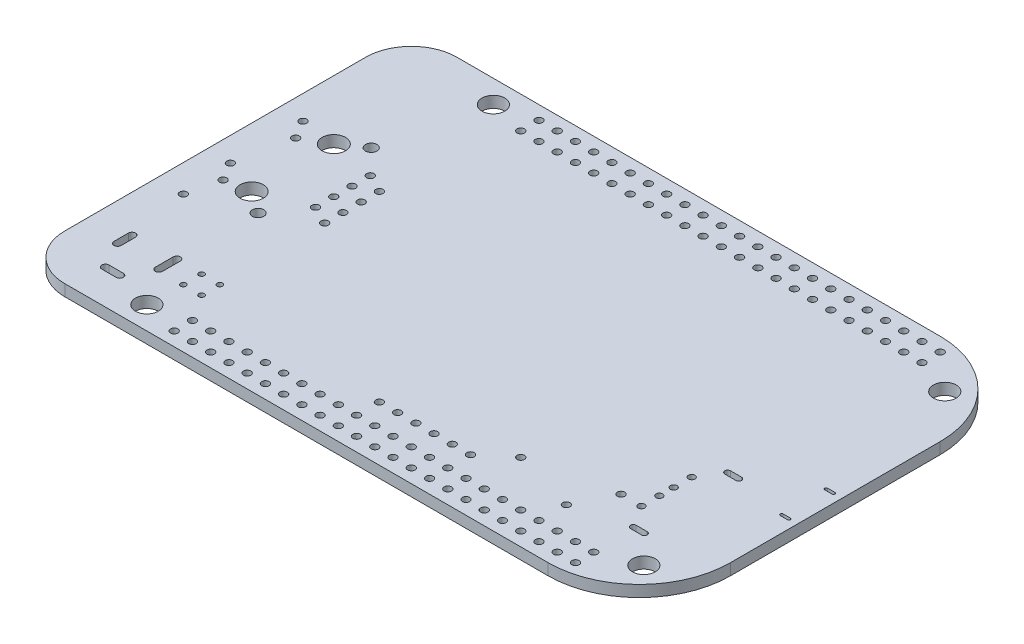
SolidWorks part; units mm, degrees
ref_plane "Front" through (0, 0, 0) normal (0, 0, 1) x (1, 0, 0)
ref_plane "Top" through (0, 0, 0) normal (0, 1, 0) x (1, 0, 0)
ref_plane "Right" through (0, 0, 0) normal (1, 0, 0) x (0, 0, -1)
sketch "Sketch2" plane through (0, 0, 0) normal (0, 1, 0) x (1, 0, 0)
  line L1 (-43.18, 27.305) -> (43.18, 27.305)
  line L2 (-43.18, 27.305) -> (-43.18, -27.305)
  line L3 (-43.18, -27.305) -> (43.18, -27.305)
  line L4 (43.18, 27.305) -> (43.18, -27.305)
  line L5 (-43.18, 27.305) -> (43.18, -27.305) construction
  line L6 (-43.18, -27.305) -> (43.18, 27.305) construction
  point P0 (0, 0)
  dimension "D1" = 86.36
  dimension "D2" = 54.61
extrude "Main Board" add sketch "Sketch2" along normal mid plane 1.5875 separate body
sketch "Sketch3" plane through (0, -0.7937, 0) normal (0, -1, 0) x (1, 0, 0)
  line L2 (43.18, -27.305) -> (-43.18, -27.305) construction
  line L3 (-43.18, -27.305) -> (-43.18, 27.305) construction
  circle A0 centre (37.465, 20.955) radius 1.5875
  circle A1 centre (37.465, -20.955) radius 1.5875
  circle A2 centre (-28.575, -24.13) radius 1.5875
  circle A3 centre (-28.575, 24.13) radius 1.5875
  dimension "D1" = 3.175
  dimension "D2" = 14.605
  dimension "D3" = 66.04
  dimension "D4" = 48.26
  dimension "D5" = 51.435
  dimension "D6" = 6.35
  dimension "D7" = 3.175
extrude "Board Mounting Holes" cut sketch "Sketch3" against normal through all contours A3 | A2 | A1 | A0
sketch "Sketch4" plane through (0, -0.7937, 0) normal (0, -1, 0) x (1, 0, 0)
  line L0 (-39.8272, -8.8646) -> (-39.8272, 1.2446) construction
  line L1 (-38.3032, -6.3246) -> (-38.3032, 3.7846) construction
  line L2 (-34.925, 3.175) -> (-34.925, -8.255) construction
  line L3 (-31.877, 5.334) -> (-31.877, -10.414) construction
  line L4 (-28.575, -6.985) -> (-28.575, 0.635) construction
  line L5 (-26.035, -5.715) -> (-26.035, 1.905) construction
  line L6 (43.18, -27.305) -> (-43.18, -27.305) construction
  line L7 (-43.18, -27.305) -> (-43.18, 27.305) construction
  circle A1 centre (-38.3032, 3.7846) radius 0.508
  circle A2 centre (-39.8272, 1.2446) radius 0.508
  circle A3 centre (-38.3032, -6.3246) radius 0.508
  circle A4 centre (-39.8272, -8.8646) radius 0.508
  circle A5 centre (-28.575, -6.985) radius 0.508
  circle A6 centre (-28.575, -4.445) radius 0.508
  circle A7 centre (-28.575, -1.905) radius 0.508
  circle A8 centre (-28.575, 0.635) radius 0.508
  circle A9 centre (-26.035, 1.905) radius 0.508
  circle A10 centre (-26.035, -0.635) radius 0.508
  circle A11 centre (-26.035, -3.175) radius 0.508
  circle A12 centre (-26.035, -5.715) radius 0.508
  circle A13 centre (-31.877, 5.334) radius 0.8001
  circle A14 centre (-34.925, 3.175) radius 1.6256
  circle A15 centre (-34.925, -8.255) radius 1.6256
  circle A16 centre (-31.877, -10.414) radius 0.8001
  dimension "D1" = 1.016
  dimension "D2" = 3.2512
  dimension "D3" = 1.6002
  dimension "D4" = 18.4404
  dimension "D5" = 10.1092
  dimension "D6" = 3.3528
  dimension "D7" = 4.8768
  dimension "D8" = 8.255
  dimension "D9" = 11.303
  dimension "D10" = 14.605
  dimension "D11" = 17.145
  dimension "D12" = 11.43
  dimension "D13" = 15.748
  dimension "D14" = 10.1092
  dimension "D15" = 20.9804
  dimension "D16" = 19.05
  dimension "D17" = 16.891
  dimension "D18" = 20.32
  dimension "D19" = 7.62
  dimension "D20" = 21.59
  dimension "D21" = 7.62
  dimension "D22" = 2.54
  dimension "D23" = 2.54
  dimension "D24" = 5.08
  dimension "D25" = 5.08
extrude "P5 - Ethernet Connector Holes" cut sketch "Sketch4" against normal through all
sketch "Sketch5" plane through (0, -0.7937, 0) normal (0, -1, 0) x (1, 0, 0)
  line L0 (30.1602, 13.9878) -> (30.1602, 6.9875) construction
  line L1 (43.18, -27.305) -> (-43.18, -27.305) construction
  line L2 (-43.18, -27.305) -> (-43.18, 27.305) construction
  line L3 (32.1004, 17.0577) -> (33.6404, 17.0577) construction
  line L4 (32.1004, 17.4545) -> (33.6404, 17.4545)
  line L5 (32.1004, 16.6608) -> (33.6404, 16.6608)
  line L6 (32.1004, 3.9177) -> (33.6404, 3.9177) construction
  line L7 (32.1004, 4.3145) -> (33.6404, 4.3145)
  line L8 (32.1004, 3.5208) -> (33.6404, 3.5208)
  circle A0 centre (30.1602, 13.9878) radius 0.46
  circle A1 centre (30.1602, 11.4884) radius 0.46
  circle A2 centre (30.1602, 9.4869) radius 0.46
  circle A3 centre (30.1602, 6.9875) radius 0.46
  arc A4 (32.1004, 17.4545) -> (32.1004, 16.6608) centre (32.1004, 17.0577) ccw
  arc A5 (33.6404, 16.6608) -> (33.6404, 17.4545) centre (33.6404, 17.0577) ccw
  arc A7 (32.1004, 4.3145) -> (32.1004, 3.5208) centre (32.1004, 3.9177) ccw
  arc A8 (33.6404, 3.5208) -> (33.6404, 4.3145) centre (33.6404, 3.9177) ccw
  point P16 (32.8704, 17.0577)
  point P23 (32.8704, 3.9177)
  dimension "D6" = 0.92
  dimension "D7" = 0.3969
  dimension "D1" = 2.4994
  dimension "D2" = 2.0015
  dimension "D3" = 2.4994
  dimension "D4" = 34.2925
  dimension "D5" = 73.3402
  dimension "D8" = 13.14
  dimension "D9" = 1.54
  dimension "D10" = 75.2804
  dimension "D11" = 31.2227
extrude "P3 - USB Host" cut sketch "Sketch5" against normal through all
sketch "Sketch6" plane through (0, -0.7937, 0) normal (0, -1, 0) x (1, 0, 0)
  line L0 (40.9621, 5.2591) -> (41.9781, 5.2591) construction
  line L1 (40.9621, 5.4575) -> (41.9781, 5.4575)
  line L2 (40.9621, 5.0606) -> (41.9781, 5.0606)
  line L3 (40.9621, -0.9411) -> (41.9781, -0.9411) construction
  line L4 (40.9621, -0.7426) -> (41.9781, -0.7426)
  line L5 (40.9621, -1.1395) -> (41.9781, -1.1395)
  line L6 (43.18, -27.305) -> (-43.18, -27.305) construction
  line L7 (-43.18, -27.305) -> (-43.18, 27.305) construction
  line L8 (41.4701, 5.2591) -> (41.4701, -0.9411) construction
  arc A0 (40.9621, 5.4575) -> (40.9621, 5.0606) centre (40.9621, 5.2591) ccw
  arc A1 (41.9781, 5.0606) -> (41.9781, 5.4575) centre (41.9781, 5.2591) ccw
  arc A2 (40.9621, -0.7426) -> (40.9621, -1.1395) centre (40.9621, -0.9411) ccw
  arc A3 (41.9781, -1.1395) -> (41.9781, -0.7426) centre (41.9781, -0.9411) ccw
  point P4 (41.4701, 5.2591)
  point P13 (41.4701, -0.9411)
  dimension "D1" = 0.1984
  dimension "D2" = 26.3639
  dimension "D3" = 6.2001
  dimension "D4" = 1.016
  dimension "D5" = 84.1421
extrude "P6 - HDMI" cut sketch "Sketch6" against normal through all
sketch "Sketch7" plane through (0, -0.7937, 0) normal (0, -1, 0) x (1, 0, 0)
  line L0 (-43.18, -27.305) -> (-43.18, 27.305) construction
  line L1 (43.18, -27.305) -> (-43.18, -27.305) construction
  circle A0 centre (32.385, 25.4) radius 0.51
  circle A2 centre (29.845, 25.4) radius 0.51
  circle A3 centre (27.305, 25.4) radius 0.51
  circle A4 centre (24.765, 25.4) radius 0.51
  circle A5 centre (22.225, 25.4) radius 0.51
  circle A6 centre (19.685, 25.4) radius 0.51
  circle A7 centre (17.145, 25.4) radius 0.51
  circle A8 centre (14.605, 25.4) radius 0.51
  circle A9 centre (12.065, 25.4) radius 0.51
  circle A10 centre (9.525, 25.4) radius 0.51
  circle A11 centre (6.985, 25.4) radius 0.51
  circle A12 centre (4.445, 25.4) radius 0.51
  circle A13 centre (1.905, 25.4) radius 0.51
  circle A14 centre (-0.635, 25.4) radius 0.51
  circle A15 centre (-3.175, 25.4) radius 0.51
  circle A16 centre (-5.715, 25.4) radius 0.51
  circle A17 centre (-8.255, 25.4) radius 0.51
  circle A18 centre (-10.795, 25.4) radius 0.51
  circle A19 centre (-13.335, 25.4) radius 0.51
  circle A20 centre (-15.875, 25.4) radius 0.51
  circle A21 centre (-18.415, 25.4) radius 0.51
  circle A22 centre (-20.955, 25.4) radius 0.51
  circle A23 centre (-23.495, 25.4) radius 0.51
  circle A24 centre (29.845, 22.86) radius 0.51
  circle A25 centre (27.305, 22.86) radius 0.51
  circle A26 centre (24.765, 22.86) radius 0.51
  circle A27 centre (22.225, 22.86) radius 0.51
  circle A28 centre (19.685, 22.86) radius 0.51
  circle A29 centre (17.145, 22.86) radius 0.51
  circle A30 centre (14.605, 22.86) radius 0.51
  circle A31 centre (12.065, 22.86) radius 0.51
  circle A32 centre (9.525, 22.86) radius 0.51
  circle A33 centre (6.985, 22.86) radius 0.51
  circle A34 centre (4.445, 22.86) radius 0.51
  circle A35 centre (1.905, 22.86) radius 0.51
  circle A36 centre (-0.635, 22.86) radius 0.51
  circle A37 centre (-3.175, 22.86) radius 0.51
  circle A38 centre (-5.715, 22.86) radius 0.51
  circle A39 centre (-8.255, 22.86) radius 0.51
  circle A40 centre (-10.795, 22.86) radius 0.51
  circle A41 centre (-13.335, 22.86) radius 0.51
  circle A42 centre (-15.875, 22.86) radius 0.51
  circle A43 centre (-18.415, 22.86) radius 0.51
  circle A44 centre (-20.955, 22.86) radius 0.51
  circle A45 centre (-23.495, 22.86) radius 0.51
  circle A46 centre (32.385, 22.86) radius 0.51
  dimension "D1" = 1.02
  dimension "D2" = 75.565
  dimension "D3" = 52.705
  dimension "D4" = 23
  dimension "D5" = 2
extrude "P9 - IDC Expansion Port" cut sketch "Sketch7" against normal through all contours A21
sketch "Sketch8" plane through (0, -0.7937, 0) normal (0, -1, 0) x (1, 0, 0)
  line L0 (43.18, -27.305) -> (-43.18, -27.305) construction
  line L1 (-43.18, -27.305) -> (-43.18, 27.305) construction
  circle A0 centre (32.385, -22.86) radius 0.51
  circle A1 centre (29.845, -22.86) radius 0.51
  circle A2 centre (27.305, -22.86) radius 0.51
  circle A3 centre (24.765, -22.86) radius 0.51
  circle A4 centre (22.225, -22.86) radius 0.51
  circle A5 centre (19.685, -22.86) radius 0.51
  circle A6 centre (17.145, -22.86) radius 0.51
  circle A7 centre (14.605, -22.86) radius 0.51
  circle A8 centre (12.065, -22.86) radius 0.51
  circle A9 centre (9.525, -22.86) radius 0.51
  circle A10 centre (6.985, -22.86) radius 0.51
  circle A11 centre (4.445, -22.86) radius 0.51
  circle A12 centre (1.905, -22.86) radius 0.51
  circle A13 centre (-0.635, -22.86) radius 0.51
  circle A14 centre (-3.175, -22.86) radius 0.51
  circle A15 centre (-5.715, -22.86) radius 0.51
  circle A16 centre (-8.255, -22.86) radius 0.51
  circle A17 centre (-10.795, -22.86) radius 0.51
  circle A18 centre (-13.335, -22.86) radius 0.51
  circle A19 centre (-15.875, -22.86) radius 0.51
  circle A20 centre (-18.415, -22.86) radius 0.51
  circle A21 centre (-20.955, -22.86) radius 0.51
  circle A22 centre (-23.495, -22.86) radius 0.51
  circle A23 centre (29.845, -25.4) radius 0.51
  circle A24 centre (27.305, -25.4) radius 0.51
  circle A25 centre (24.765, -25.4) radius 0.51
  circle A26 centre (22.225, -25.4) radius 0.51
  circle A27 centre (19.685, -25.4) radius 0.51
  circle A28 centre (17.145, -25.4) radius 0.51
  circle A29 centre (14.605, -25.4) radius 0.51
  circle A30 centre (12.065, -25.4) radius 0.51
  circle A31 centre (9.525, -25.4) radius 0.51
  circle A32 centre (6.985, -25.4) radius 0.51
  circle A33 centre (4.445, -25.4) radius 0.51
  circle A34 centre (1.905, -25.4) radius 0.51
  circle A35 centre (-0.635, -25.4) radius 0.51
  circle A36 centre (-3.175, -25.4) radius 0.51
  circle A37 centre (-5.715, -25.4) radius 0.51
  circle A38 centre (-8.255, -25.4) radius 0.51
  circle A39 centre (-10.795, -25.4) radius 0.51
  circle A40 centre (-13.335, -25.4) radius 0.51
  circle A41 centre (-15.875, -25.4) radius 0.51
  circle A42 centre (-18.415, -25.4) radius 0.51
  circle A43 centre (-20.955, -25.4) radius 0.51
  circle A44 centre (-23.495, -25.4) radius 0.51
  circle A45 centre (32.385, -25.4) radius 0.51
  dimension "D1" = 1.02
  dimension "D2" = 4.445
  dimension "D3" = 75.565
  dimension "D4" = 23
  dimension "D5" = 2
extrude "P8 - IDC Expansion Port" cut sketch "Sketch8" against normal through all
sketch "Sketch9" plane through (0, -0.7937, 0) normal (0, -1, 0) x (1, 0, 0)
  line L0 (43.18, -27.305) -> (-43.18, -27.305) construction
  line L1 (-43.18, -27.305) -> (-43.18, 27.305) construction
  circle A0 centre (15.875, 16.51) radius 0.508
  dimension "D1" = 1.016
  dimension "D2" = 43.815
  dimension "D3" = 59.055
extrude "TP1 - Test Point 1" cut sketch "Sketch9" against normal through all
sketch "Sketch10" plane through (0, -0.7937, 0) normal (0, -1, 0) x (1, 0, 0)
  line L0 (-43.18, -27.305) -> (-43.18, 27.305) construction
  line L2 (-43.18, 27.305) -> (43.18, 27.305) construction
  circle A0 centre (-39.37, 8.255) radius 0.508
  dimension "D3" = 1.016
  dimension "D1" = 3.81
  dimension "D2" = 19.05
extrude "TP4 - Test Point 4" cut sketch "Sketch10" against normal through all
sketch "Sketch11" plane through (0, -0.7937, 0) normal (0, -1, 0) x (1, 0, 0)
  line L0 (-43.18, 27.305) -> (43.18, 27.305) construction
  line L1 (-43.18, -27.305) -> (-43.18, 27.305) construction
  circle A0 centre (27.305, 13.97) radius 0.508
  circle A1 centre (24.765, 19.05) radius 0.508
  dimension "D1" = 1.016
  dimension "D2" = 5.08
  dimension "D3" = 2.54
  dimension "D4" = 8.255
  dimension "D5" = 67.945
extrude "RT1 - Capacitor" cut sketch "Sketch11" against normal through all
sketch "Sketch12" plane through (0, -0.7937, 0) normal (0, -1, 0) x (1, 0, 0)
  line L0 (-43.18, 27.305) -> (43.18, 27.305) construction
  line L1 (-43.18, -27.305) -> (-43.18, 27.305) construction
  circle A0 centre (12.065, 19.685) radius 0.508
  circle A1 centre (9.525, 19.685) radius 0.508
  circle A2 centre (6.985, 19.685) radius 0.508
  circle A3 centre (4.445, 19.685) radius 0.508
  circle A4 centre (1.905, 19.685) radius 0.508
  circle A5 centre (-0.635, 19.685) radius 0.508
  dimension "D1" = 1.016
  dimension "D2" = 7.62
  dimension "D3" = 55.245
  dimension "D4" = 6
extrude "J1 - Debug Port" cut sketch "Sketch12" against normal through all
sketch "Sketch13" plane through (0, -0.7937, 0) normal (0, -1, 0) x (1, 0, 0)
  line L0 (-32.004, 19.03) -> (-32.004, 16.53) construction
  line L1 (-31.5036, 19.03) -> (-31.5036, 16.53)
  line L2 (-32.5044, 19.03) -> (-32.5044, 16.53)
  line L3 (-37.9984, 16.78) -> (-37.9984, 18.78) construction
  line L4 (-38.4984, 16.78) -> (-38.4984, 18.78)
  line L5 (-37.4984, 16.78) -> (-37.4984, 18.78)
  line L6 (-36.0012, 22.479) -> (-34.0012, 22.479) construction
  line L7 (-36.0012, 22.9794) -> (-34.0012, 22.9794)
  line L8 (-36.0012, 21.9786) -> (-34.0012, 21.9786)
  line L9 (-43.18, 27.305) -> (43.18, 27.305) construction
  line L10 (-43.18, -27.305) -> (-43.18, 27.305) construction
  arc A0 (-31.5036, 19.03) -> (-32.5044, 19.03) centre (-32.004, 19.03) ccw
  arc A1 (-32.5044, 16.53) -> (-31.5036, 16.53) centre (-32.004, 16.53) ccw
  arc A2 (-38.4984, 16.78) -> (-37.4984, 16.78) centre (-37.9984, 16.78) ccw
  arc A3 (-37.4984, 18.78) -> (-38.4984, 18.78) centre (-37.9984, 18.78) ccw
  arc A4 (-36.0012, 22.9794) -> (-36.0012, 21.9786) centre (-36.0012, 22.479) ccw
  arc A5 (-34.0012, 21.9786) -> (-34.0012, 22.9794) centre (-34.0012, 22.479) ccw
  point P4 (-32.004, 17.78)
  point P9 (-37.9984, 17.78)
  point P18 (-35.0012, 22.479)
  dimension "D1" = 0.5
  dimension "D2" = 0.5004
  dimension "D3" = 0.5004
  dimension "D4" = 5.9944
  dimension "D5" = 2.5
  dimension "D6" = 2
  dimension "D7" = 2
  dimension "D8" = 4.826
  dimension "D9" = 8.1788
  dimension "D10" = 9.525
  dimension "D11" = 5.1816
extrude "P1 - Power Plug" cut sketch "Sketch13" against normal through all
sketch "Sketch14" plane through (0, -0.7937, 0) normal (0, -1, 0) x (1, 0, 0)
  line L0 (-43.18, 27.305) -> (43.18, 27.305) construction
  line L3 (-43.18, -27.305) -> (-43.18, 27.305) construction
  circle A0 centre (-28.448, 19.177) radius 0.381
  dimension "D1" = 0.762
  dimension "D2" = 8.128
  dimension "D3" = 14.732
extrude "TP6 - BATTERY" cut sketch "Sketch14" against normal through all
sketch "Sketch15" plane through (0, -0.7937, 0) normal (0, -1, 0) x (1, 0, 0)
  line L0 (-43.18, -27.305) -> (-43.18, 27.305) construction
  line L1 (-43.18, 27.305) -> (43.18, 27.305) construction
  circle A0 centre (-25.908, 19.177) radius 0.381
  dimension "D1" = 0.762
  dimension "D2" = 17.272
  dimension "D3" = 8.128
extrude "TP8 - BATTERY" cut sketch "Sketch15" against normal through all
sketch "Sketch16" plane through (0, -0.7937, 0) normal (0, -1, 0) x (1, 0, 0)
  line L0 (-43.18, -27.305) -> (-43.18, 27.305) construction
  line L1 (-43.18, 27.305) -> (43.18, 27.305) construction
  circle A0 centre (-28.448, 16.637) radius 0.381
  dimension "D1" = 0.762
  dimension "D2" = 14.732
  dimension "D3" = 10.668
extrude "TP5 - BATTERY" cut sketch "Sketch16" against normal through all
sketch "Sketch18" plane through (0, -0.7937, 0) normal (0, -1, 0) x (1, 0, 0)
  line L0 (-43.18, -27.305) -> (-43.18, 27.305) construction
  line L1 (-43.18, 27.305) -> (43.18, 27.305) construction
  circle A0 centre (-25.908, 16.637) radius 0.381
  dimension "D1" = 0.762
  dimension "D2" = 17.272
  dimension "D3" = 10.668
extrude "TP7 - BATTERY" cut sketch "Sketch18" against normal through all
fillet "Fillet1" radius 6.35 2 edges at (-43.18, 0, -27.305) (-43.18, 0, 27.305)
fillet "Fillet2" radius 12.7 2 edges at (43.18, 0, 27.305) (43.18, 0, -27.305)
